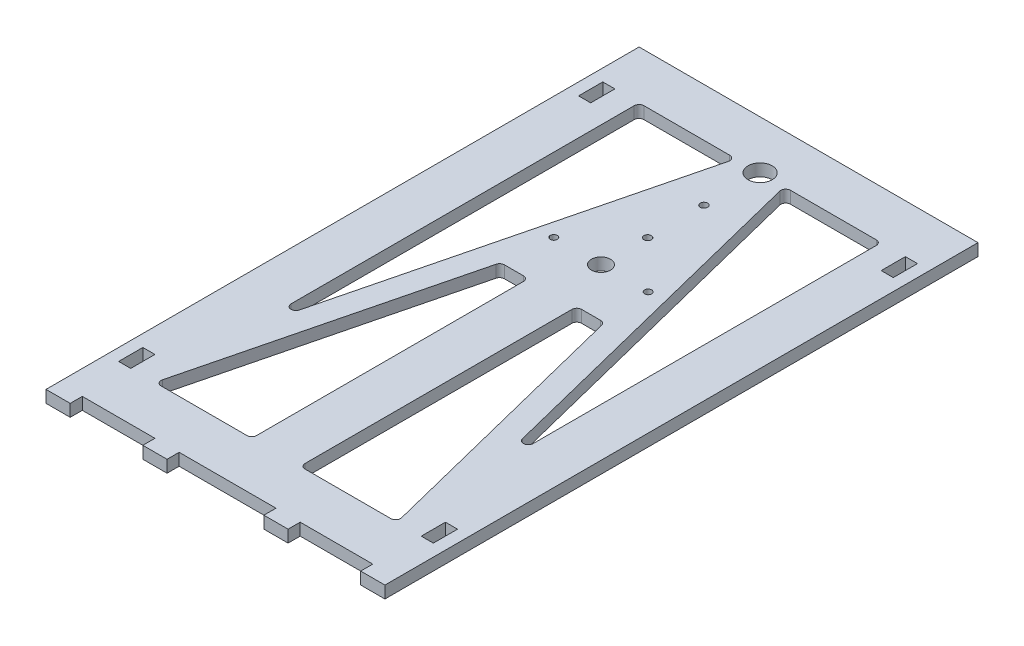
SolidWorks part; units mm, degrees
material "Beech"
ref_plane "Front Plane" through (0, 0, 0) normal (0, 0, 1) x (1, 0, 0)
ref_plane "Top Plane" through (0, 0, 0) normal (0, 1, 0) x (1, 0, 0)
ref_plane "Right Plane" through (0, 0, 0) normal (1, 0, 0) x (0, 0, -1)
sketch "Sketch1" plane through (0, 0, 0) normal (0, 1, 0) x (1, 0, 0)
  line L0 (0, 0) -> (177.8, 0)
  line L1 (0, 0) -> (0, 304.8)
  line L2 (177.8, 0) -> (177.8, 304.8)
  line L3 (0, 304.8) -> (177.8, 304.8)
  line L4 (0, 0) -> (12.7, 0)
  line L5 (0, 0) -> (0, -6.35)
  line L6 (12.7, 0) -> (12.7, -6.35)
  line L7 (0, -6.35) -> (12.7, -6.35)
  line L8 (177.8, 0) -> (165.1, 0)
  line L9 (177.8, 0) -> (177.8, -6.35)
  line L10 (165.1, 0) -> (165.1, -6.35)
  line L11 (177.8, -6.35) -> (165.1, -6.35)
  line L12 (127, 0) -> (114.3, 0)
  line L13 (127, 0) -> (127, -6.35)
  line L14 (114.3, 0) -> (114.3, -6.35)
  line L15 (127, -6.35) -> (114.3, -6.35)
  line L16 (50.8, 0) -> (63.5, 0)
  line L17 (50.8, 0) -> (50.8, -6.35)
  line L18 (63.5, 0) -> (63.5, -6.35)
  line L19 (50.8, -6.35) -> (63.5, -6.35)
  line L20 (165.1, 279.4) -> (171.45, 279.4)
  line L21 (165.1, 279.4) -> (165.1, 266.7)
  line L22 (171.45, 279.4) -> (171.45, 266.7)
  line L23 (165.1, 266.7) -> (171.45, 266.7)
  line L24 (6.35, 279.4) -> (12.7, 279.4)
  line L25 (6.35, 279.4) -> (6.35, 266.7)
  line L26 (12.7, 279.4) -> (12.7, 266.7)
  line L27 (6.35, 266.7) -> (12.7, 266.7)
  line L28 (6.35, 38.1) -> (12.7, 38.1)
  line L29 (6.35, 38.1) -> (6.35, 25.4)
  line L30 (12.7, 38.1) -> (12.7, 25.4)
  line L31 (6.35, 25.4) -> (12.7, 25.4)
  line L32 (165.1, 38.1) -> (171.45, 38.1)
  line L33 (165.1, 38.1) -> (165.1, 25.4)
  line L34 (171.45, 38.1) -> (171.45, 25.4)
  line L35 (165.1, 25.4) -> (171.45, 25.4)
  line L36 (76.2, 279.4) -> (25.4, 279.4)
  line L37 (25.4, 279.4) -> (25.4, 76.2)
  line L38 (25.4, 76.2) -> (76.2, 279.4)
  line L39 (101.6, 279.4) -> (152.4, 279.4)
  line L40 (152.4, 279.4) -> (152.4, 76.2)
  line L41 (152.4, 76.2) -> (101.6, 279.4)
  line L42 (25.4, 25.4) -> (61.675, 170.5)
  line L43 (61.675, 170.5) -> (76.2, 170.5)
  line L44 (76.2, 170.5) -> (76.2, 25.4)
  line L45 (76.2, 25.4) -> (25.4, 25.4)
  line L46 (101.6, 170.5) -> (116.125, 170.5)
  line L47 (116.125, 170.5) -> (152.4, 25.4)
  line L48 (152.4, 25.4) -> (101.6, 25.4)
  line L49 (101.6, 25.4) -> (101.6, 170.5)
  circle A0 centre (88.9, 279.4) radius 6.35
  circle A1 centre (88.9, 249.9) radius 1.935
  circle A2 centre (88.9, 220.4) radius 1.935
  circle A3 centre (88.9, 195.9) radius 5
  circle A4 centre (113.65, 195.9) radius 1.8542
  circle A5 centre (64.15, 195.9) radius 1.8542
  point P21 (88.9, 304.8)
  dimension "D8" = 12.7
  dimension "D14" = 3.87
  dimension "D15" = 3.87
  dimension "D18" = 10
  dimension "D19" = 3.7084
  dimension "D1" = 177.8
  dimension "D2" = 6.35
  dimension "D3" = 12.7
  dimension "D4" = 50.8
  dimension "D5" = 50.8
  dimension "D6" = 304.8
  dimension "D7" = 25.4
  dimension "D9" = 25.4
  dimension "D10" = 25.4
  dimension "D11" = 50.8
  dimension "D12" = 12.7
  dimension "D13" = 12.7
  dimension "D16" = 29.5
  dimension "D17" = 29.5
  dimension "D20" = 24.75
  dimension "D21" = 24.75
  dimension "D22" = 24.5
  dimension "D23" = 203.2
  dimension "D24" = 25.4
extrude "Front Panel" add sketch "Sketch1" along normal blind 6.35
fillet "Fillet1" radius 2.54 14 edges at (152.4, 3.175, -76.2) (152.4, 3.175, -279.4) (101.6, 3.175, -279.4) (76.2, 3.175, -279.4) (25.4, 3.175, -279.4) (25.4, 3.175, -76.2) (152.4, 3.175, -25.4) (101.6, 3.175, -25.4) (76.2, 3.175, -25.4) (25.4, 3.175, -25.4) (61.675, 3.175, -170.5) (76.2, 3.175, -170.5) (116.125, 3.175, -170.5) (101.6, 3.175, -170.5)
equation "\"CageLeftBottomEdge\"=22.11mm"
equation "\"CageLeftTopEdge\"=22.11mm"
equation "\"CageRightBottomEdge\"=21.63mm"
equation "\"CageRightTopEdge\"=21.63mm"
equation "\"CageHeight\"=86.04mm"
equation "\"CageLength\"=73.76mm"
equation "\"CageTopScrewClearance\"=10mm"
equation "\"CageBottomScrewClearance\"=25mm"
equation "\"CageLeftTopDepth\"= 11.65mm"
equation "\"CageLeftBottomDepth\"=11.11mm"
equation "\"CageLeftTopHeight\"=8.56175mm"
equation "\"CageLeftBottomHeight\"=16mm"
equation "\"CageRightTopDepth\"= 11.05mm"
equation "\"CageRightBottomDepth\"=10.58mm"
equation "\"CageRightTopHeight\"=9.6mm"
equation "\"CageRightBottomHeight\"=15.49mm"
equation "\"CageLeftTopChannelDepth\"=2.41908mm"
equation "\"CageLeftBottomChannelDepth\"=2.588mm"
equation "\"CageLeftChannelHeight\"=11.7mm"
equation "\"CageRightTopChannelDepth\"=2.32mm"
equation "\"CageRightBottomChannelDepth\"=2.318mm"
equation "\"CageRightChannelHeight\"=10mm"
equation "\"CageChanRelHeight\"=23.99mm"
equation "\"CageChanRelDepth\"=5.492mm"
equation "\"CageChamberRadius\"=16.261mm"
equation "\"CageScrewDiameter\"=4.8mm"
equation "\"CageSetScrewDiameter\"=3.5mm"
equation "\"CageAxleRadius\"=6.639mm"
equation "\"CageAxleKeyHeight\"=1.619mm"
equation "\"CageAxleKeyWidth\"=2.662mm"
equation "\"CageHoseWindowWidth\"=16.29mm"
equation "\"CageHoseWindowHeight\"=26.5mm"
equation "\"CageHoseWindow-Edge\"=8.89mm"
equation "\"CageScrew-VerticalEdge\"=5.0mm"
equation "\"CageScrew-HorizontalEdge\"=7.5mm"
equation "\"CageScrew-HoseCornerScrewEdge\"=4.45mm"
equation "\"CageAxle-BottomEdge\"=56.05mm"
equation "\"CageAxle-FrontEdge\"=46.03mm"
equation "\"CageBackSetScrew-Axle\"=40mm"
equation "\"CageFrontSetScrew-Axle\"=22mm"
equation "\"CageVelocityWindow-BackEdge\"=34.8mm"
equation "\"CageVelocityWindow-BottomEdge\"=27.55mm"
equation "\"CageVelocityWindowHeight\"=22.29mm"
equation "\"CageVelocityWindowWidth\"=12.61mm"
equation "\"TriggerSlot-BottomEdge\"=6.35mm"
equation "\"TriggerSlot-FrontEdge\"=15mm"
equation "\"TriggerSlotSize\"=6.7mm"
equation "\"TriggerRackOffset\"=6mm"
equation "\"TriggerSlotSizeInt\"=.25in"
equation "\"MotorMountLegLength\"=.25in"
equation "\"GearOffset\"=.264907in"
equation "\"TriggerSlotSpacing\"=.25in"
equation "\"TriggerMiniSlotWidth\"=3.5mm"
equation "\"TriggerRackWidth\"=6.5mm"
equation "\"pandiscradius\"=14in"
equation "\"towermaterialwidth\"=.25in"
equation "\"towerslotlength\"=.5in"
equation "\"towermarkerspace\"=5in"
equation "\"towerslothorizoffset\"=1in"
equation "\"towerslothorizspacing\"=2in"
equation "\"towerslotvertoffset\"=3in"
equation "\"towerslotvertspacing\"=1in"
equation "\"towerheight\"=12in"
equation "\"towerupslot\"=1in"
equation "\"D1@Sketch1\"=(\"towerslothorizoffset\"+\"towerslothorizspacing\"+\"towerslotlength\")*2"
equation "\"D2@Sketch1\"=\"towermaterialwidth\""
equation "\"D3@Sketch1\"=\"towerslotlength\""
equation "\"D4@Sketch1\"=\"towerslothorizspacing\""
equation "\"D5@Sketch1\"=\"towerslothorizspacing\""
equation "\"D6@Sketch1\"=\"towerheight\""
equation "\"D7@Sketch1\"=\"towerupslot\""
equation "\"toweraxle\"=.5in"
equation "\"D8@Sketch1\"=\"toweraxle\""
equation "\"D9@Sketch1\"=\"towerupslot\""
equation "\"D10@Sketch1\"= \"towerupslot\""
equation "\"D1@Front Panel\"=\"towermaterialwidth\""
equation "\"stepperouterrad\"=10mm"
equation "\"stepperscrewsize\"=3.45mm"
equation "\"stepperscrewc2c\"=49.5mm"
equation "\"stepperdepthoffset\"=24mm"
equation "\"stepperhorizoffset\"=22.91mm"
equation "\"shaftslotOD\"=18.8mm"
equation "\"shaftslotID\"=13.28mm"
equation "\"shaftkeywidth\"=2.67mm"
equation "\"shaftkeydepth\"=1.8mm"
equation "\"shaftcollartotaldepth\"=12.5mm"
equation "\"shaftsquaredepth\"=6mm"
equation "\"shaftsetscrewsize\"=3.5mm"
equation "\"shaftkeytightdepth\"=1.85mm"
equation "\"shaftslottightID\"=12.78mm"
equation "\"shaftsetscrewoffset\"=9mm"
equation "\"cagecollartotaldepth\"=10mm"
equation "\"cagecollartotalwidth\"=35mm"
equation "\"cagecollarbasedepth\"=4mm"
equation "\"ajaxaxlesize\"=3.87mm"
equation "\"D14@Sketch1\"=\"ajaxaxlesize\""
equation "\"D15@Sketch1\"=\"ajaxaxlesize\""
equation "\"ajax4020gap\"=29.5mm"
equation "\"D16@Sketch1\"=\"ajax4020gap\""
equation "\"D17@Sketch1\"=\"ajax4020gap\""
equation "\"D18@Sketch1\"=\"stepperouterrad\""
equation "\"D19@Sketch1\"=\"no6diam\""
equation "\"D20@Sketch1\"=\"stepperscrewc2c\"/2"
equation "\"D21@Sketch1\"=\"stepperscrewc2c\"/2"
equation "\"ajax4010gap\"=24.5mm"
equation "\"D22@Sketch1\"=\"ajax4010gap\""
equation "\"towerspeedwidth\"=2in"
equation "\"towerspeedheight\"=8in"
equation "\"towerspeedgap\"=2in"
equation "\"stepperaxleflat\"=.037in"
equation "\"stepperaxlerad\"=0.11811024in"
equation "\"ajaxinnercut\"=2.3mm"
equation "\"ajaxwidth\"=6.1mm"
equation "\"ajaxdiametral\"=25.8854"
equation "\"ajaxcutoutdepth\"=2.3mm"
equation "\"ajax20hubbuffer\"=6.1mm"
equation "\"ajax20hubholeoffset\"=.19685in"
equation "\"ajax20hubholesize\"=.059055in"
equation "\"ajax20cutoutint\"=13.4mm"
equation "\"ajax40hubholesize\"=7.21mm"
equation "\"ajax40hubholeoffset\"=10mm"
equation "\"ajax40hubbuffer\"=8.9mm"
equation "\"ajax40cutoutint\"=32.6mm"
equation "\"bearingpandiscrad\"=6.8in"
equation "\"bearingpandiscang\"=48.75deg"
equation "\"bearingclearholedist\"=4.7345in"
equation "\"bearingclearholesize\"=.5in"
equation "\"bearingclearholeang\"=22.5deg"
equation "\"bearingmountholedist\"=4.25in"
equation "\"bearingwirehole\"=1.5in"
equation "\"no6diam\"=.146in"
equation "\"D23@Sketch1\"=\"towerspeedheight\""
equation "\"D11@Sketch1\"=\"towerspeedwidth\""
equation "\"D24@Sketch1\"=2*\"toweraxle\""
equation "\"D12@Sketch1\"=\"toweraxle\""
equation "\"D13@Sketch1\"=\"toweraxle\""
equation "\"gearhubintdiam\"=30mm"
equation "\"gearhubintwid\"=15mm"
equation "\"shortconangle\"=20deg"
equation "\"shortconlen\"=.875in"
equation "\"longconlen\"=1.25in"
equation "\"longconangle\"=15deg"
